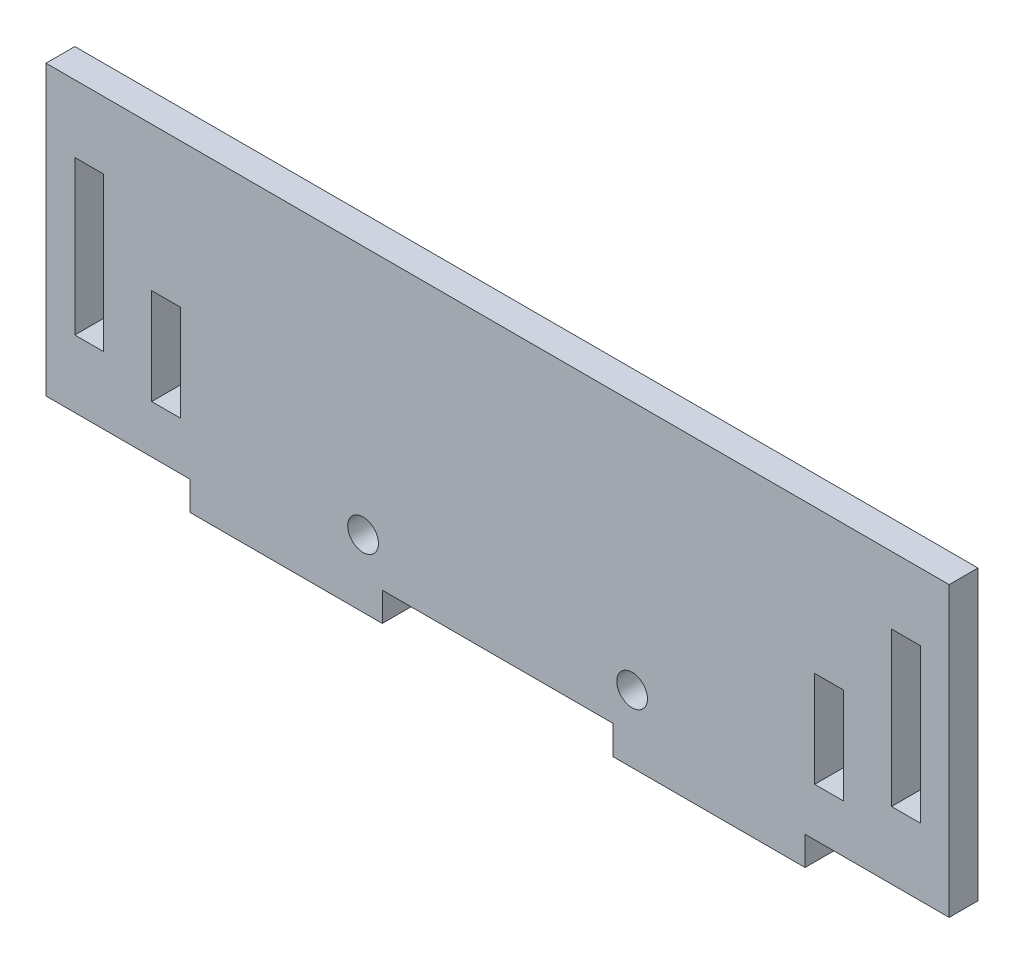
SolidWorks part; units mm, degrees
ref_plane "前视基准面" through (0, 0, 0) normal (0, 0, 1) x (1, 0, 0)
ref_plane "上视基准面" through (0, 0, 0) normal (0, 1, 0) x (1, 0, 0)
ref_plane "右视基准面" through (0, 0, 0) normal (1, 0, 0) x (0, 0, -1)
sketch "草图1" plane through (0, 0, 0) normal (0, 0, 1) x (1, 0, 0)
  line L0 (44, 0) -> (44, 4)
  line L1 (0, 0) -> (12, 0)
  line L2 (0, 7) -> (0, 30)
  line L3 (0, 30) -> (88, 30)
  line L4 (88, 7) -> (88, 30)
  line L5 (44, 4) -> (53.45, 4)
  line L6 (55, 4) -> (44, 4)
  line L7 (44, 4) -> (33, 4)
  line L8 (0, 0) -> (12, 0)
  line L9 (12, 0) -> (12, -3)
  line L10 (12, -3) -> (32, -3)
  line L11 (32, -3) -> (32, 0)
  line L12 (88, 0) -> (76, 0)
  line L13 (76, 0) -> (76, -3)
  line L14 (76, -3) -> (56, -3)
  line L15 (56, -3) -> (56, 0)
  line L16 (76, 0) -> (88, 0)
  line L18 (88, 15) -> (88, 23)
  line L19 (88, 23) -> (85, 23)
  line L20 (85, 15) -> (85, 23)
  line L22 (88, 15) -> (88, 7)
  line L23 (88, 7) -> (85, 7)
  line L24 (85, 15) -> (85, 7)
  line L25 (88, 30) -> (91, 30)
  line L26 (88, 30) -> (88, 7)
  line L27 (88, 0) -> (91, 0)
  line L28 (91, 30) -> (91, 0)
  line L30 (0, 15) -> (0, 23)
  line L31 (0, 23) -> (3, 23)
  line L32 (3, 15) -> (3, 23)
  line L34 (0, 15) -> (0, 7)
  line L35 (0, 7) -> (3, 7)
  line L36 (3, 15) -> (3, 7)
  line L37 (0, 30) -> (-3, 30)
  line L38 (0, 30) -> (0, 7)
  line L39 (0, 0) -> (-3, 0)
  line L40 (-3, 30) -> (-3, 0)
  line L41 (32, 0) -> (56, 0)
  line L42 (44, 4) -> (58, 4)
  line L43 (58, 4) -> (44, 4)
  line L44 (44, 4) -> (30, 4)
  line L45 (85, 15) -> (80, 15)
  line L46 (3, 15) -> (8, 15)
  line L47 (80, 15) -> (77, 15)
  line L48 (80, 15) -> (80, 5)
  line L49 (80, 5) -> (77, 5)
  line L50 (77, 15) -> (77, 5)
  line L56 (8, 15) -> (11, 15)
  line L57 (8, 15) -> (8, 5)
  line L58 (8, 5) -> (11, 5)
  line L59 (11, 15) -> (11, 5)
  circle A2 centre (58, 4) radius 1.6
  circle A3 centre (30, 4) radius 1.6
extrude "凸台-拉伸1" add sketch "草图1" along normal blind 3
